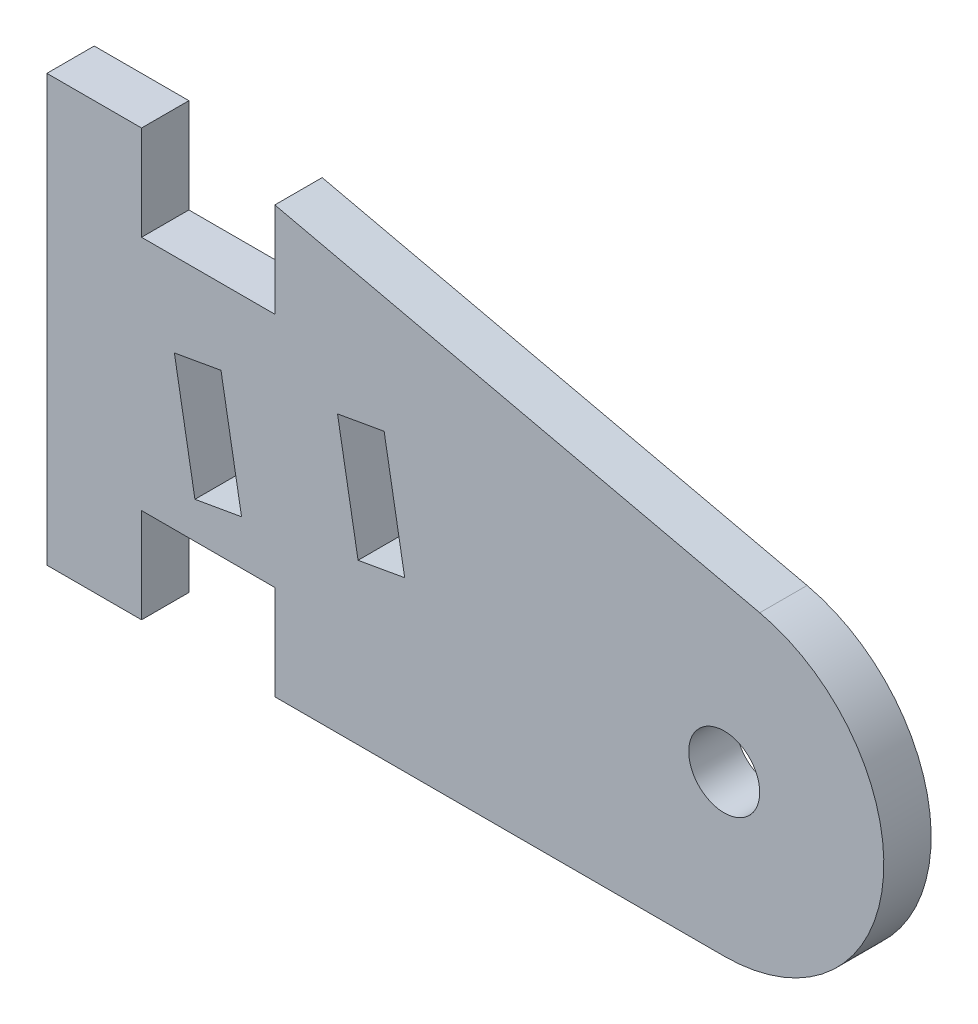
SolidWorks part; units mm, degrees
ref_plane "Front Plane" through (0, 0, 0) normal (0, 0, 1) x (1, 0, 0)
ref_plane "Top Plane" through (0, 0, 0) normal (0, 1, 0) x (1, 0, 0)
ref_plane "Right Plane" through (0, 0, 0) normal (1, 0, 0) x (0, 0, -1)
sketch "Sketch1" plane through (0, 0, 0) normal (0, 0, 1) x (1, 0, 0)
  line L0 (0, 0) -> (0, 18.0003)
  line L1 (9.6315, 0) -> (9.6315, 4)
  line L2 (9.6315, 4) -> (4, 4)
  line L3 (9.6315, 18.0003) -> (30.1232, 13.3208)
  line L4 (9.6315, 18.0003) -> (9.6315, 14.0003)
  line L5 (9.6315, 14.0003) -> (4, 14.0003)
  line L6 (0, 0) -> (4, 0)
  line L7 (4, 0) -> (4, 4)
  line L9 (14.2505, 12.0256) -> (12.2808, 11.6783)
  line L10 (7.3568, 10.81) -> (8.225, 5.886)
  line L11 (7.3568, 10.81) -> (5.3872, 10.4627)
  line L12 (4, 18.0003) -> (4, 14.0003)
  line L13 (0, 18.0003) -> (4, 18.0003)
  line L14 (5.3872, 10.4627) -> (6.2554, 5.5387)
  line L15 (6.2554, 5.5387) -> (8.225, 5.886)
  line L16 (12.2808, 11.6783) -> (13.1491, 6.7542)
  line L17 (13.1491, 6.7542) -> (15.1187, 7.1015)
  line L18 (14.2505, 12.0256) -> (15.1187, 7.1015)
  line L20 (9.6315, 0) -> (28.6215, 0)
  circle A0 centre (28.6215, 6.745) radius 12.12 construction
  arc A1 (28.6215, 0) -> (30.1232, 13.3208) centre (28.6215, 6.745) ccw
  circle A5 centre (28.6215, 6.745) radius 1.5
  dimension "D1" = 3
  dimension "D2" = 6.745
  dimension "D12" = 24.24
  dimension "D4" = 5.3872
  dimension "D5" = 6.2554
  dimension "D6" = 7.3568
  dimension "D7" = 12.2808
  dimension "D10" = 5.5387
  dimension "D11" = 5.886
  dimension "ThumbLinkLengthMCP" = 18.99
  dimension "D8" = 18.0003
  dimension "D9" = 5.6315
  dimension "D13" = 9.6315
extrude "Boss-Extrude1" add sketch "Sketch1" along normal blind 2
equation "\"ThumbLinkLengthMCP@Sketch1\"= \"HB@parametersSketch@prostheticParameters.SLDPRT\" * 0.211"
